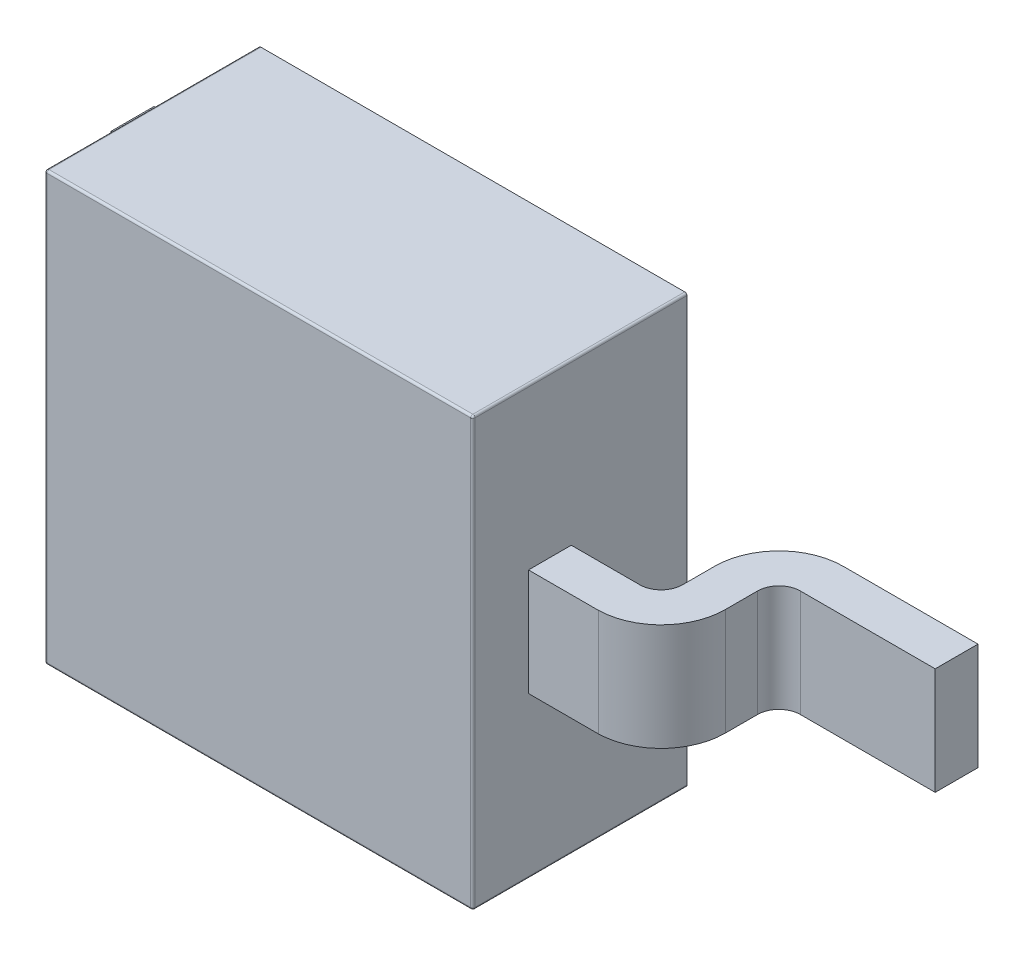
SolidWorks part; units mm, degrees
ref_plane "Front Plane" through (0, 0, 0) normal (0, 0, 1) x (1, 0, 0)
ref_plane "Top Plane" through (0, 0, 0) normal (0, 1, 0) x (1, 0, 0)
ref_plane "Right Plane" through (0, 0, 0) normal (1, 0, 0) x (0, 0, -1)
ref_plane "Plane1" through (0, 0, 0.01) normal (0, 0, 1) x (1, 0, 0)
sketch "Sketch1" plane through (0, 0, 0.01) normal (0, 0, 1) x (1, 0, 0)
  line L1 (-1, 1) -> (1, 1)
  line L2 (-1, 1) -> (-1, -1)
  line L3 (-1, -1) -> (1, -1)
  line L4 (1, 1) -> (1, -1)
extrude "Extrude1" add sketch "Sketch1" along normal blind 1
sketch "Sketch2" plane through (0, 0, 0) normal (0, 0, 1) x (1, 0, 0)
  line L1 (-1.5, 0.5) -> (0.5, 0.5)
  line L2 (-1.5, 0.5) -> (-1.5, -0.5)
  line L3 (-1.5, -0.5) -> (0.5, -0.5)
  line L4 (0.5, 0.5) -> (0.5, -0.5)
extrude "Extrude2" add sketch "Sketch2" along normal blind 0.2
sketch "Sketch3" plane through (0, 0, 0) normal (0, 0, 1) x (1, 0, 0)
  line L0 (1, -1) -> (1, 1) construction
  line L1 (1, 0.25) -> (2.35, 0.25)
  line L2 (1, 0.25) -> (1, -0.25)
  line L3 (1, -0.25) -> (2.35, -0.25)
  line L4 (2.35, 0.25) -> (2.35, -0.25)
extrude "Extrude3" add sketch "Sketch3" along normal blind 0.75
sketch "Sketch4" plane through (0, -0.25, 0) normal (0, -1, 0) x (1, 0, 0)
  line L0 (2.35, 0.2) -> (2.35, 0.75)
  line L1 (2.35, 0.2) -> (1.72, 0.2)
  line L2 (2.35, 0.75) -> (2.35, 0) construction
  line L3 (1.62, 0.75) -> (1, 0.75) construction
  line L4 (1, 0.75) -> (2.35, 0.75) construction
  line L5 (1.32, 0.5501) -> (1, 0.5501)
  line L6 (1.42, 0.3) -> (1.42, 0.4501)
  line L7 (1.62, 0.5501) -> (1, 0.5501) construction
  line L8 (1.62, 0.4501) -> (1.62, 0.3)
  line L9 (2.35, 0.75) -> (1.32, 0.7501)
  line L10 (1, 0.5501) -> (1, 0)
  line L11 (1, 0) -> (1.72, 0)
  arc A0 (1.72, 0.2) -> (1.62, 0.3) centre (1.72, 0.3) cw
  arc A1 (1.42, 0.4501) -> (1.32, 0.5501) centre (1.32, 0.4501) ccw
  arc A2 (1.72, 0) -> (1.42, 0.3) centre (1.72, 0.3) cw
  arc A3 (1.62, 0.4501) -> (1.32, 0.7501) centre (1.32, 0.4501) ccw
  point P16 (1.62, 0.75)
extrude "Extrude4" cut sketch "Sketch4" against normal through all
fillet "Fillet1" radius 0.01 8 edges at (-1, 1, 0.51) (-1, 0, 1.01) (-1, -1, 0.51) (1, -1, 0.51) (1, 0, 1.01) (1, 1, 0.51) (0, 1, 1.01) (0, -1, 1.01)
